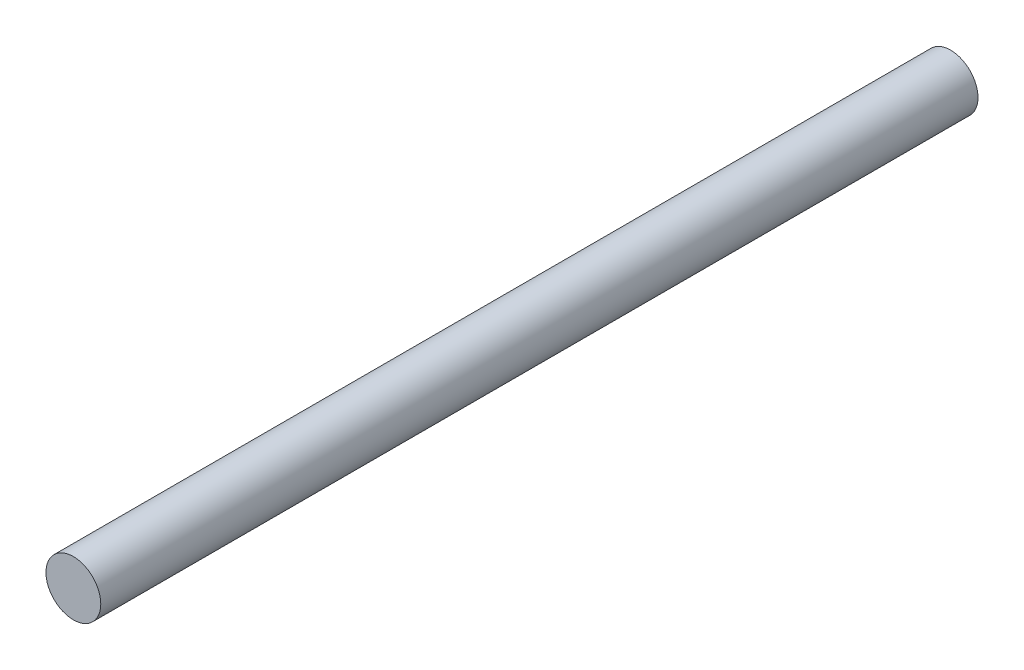
SolidWorks part; units mm, degrees
ref_plane "Front" through (0, 0, 0) normal (0, 0, 1) x (1, 0, 0)
ref_plane "Top" through (0, 0, 0) normal (0, 1, 0) x (1, 0, 0)
ref_plane "Right" through (0, 0, 0) normal (1, 0, 0) x (0, 0, -1)
sketch "Sketch1" plane through (0, 0, 0) normal (0, 0, 1) x (1, 0, 0)
  circle A0 centre (0, 0) radius 6.35
extrude "Boss-Extrude1" add sketch "Sketch1" along normal blind 203.2
